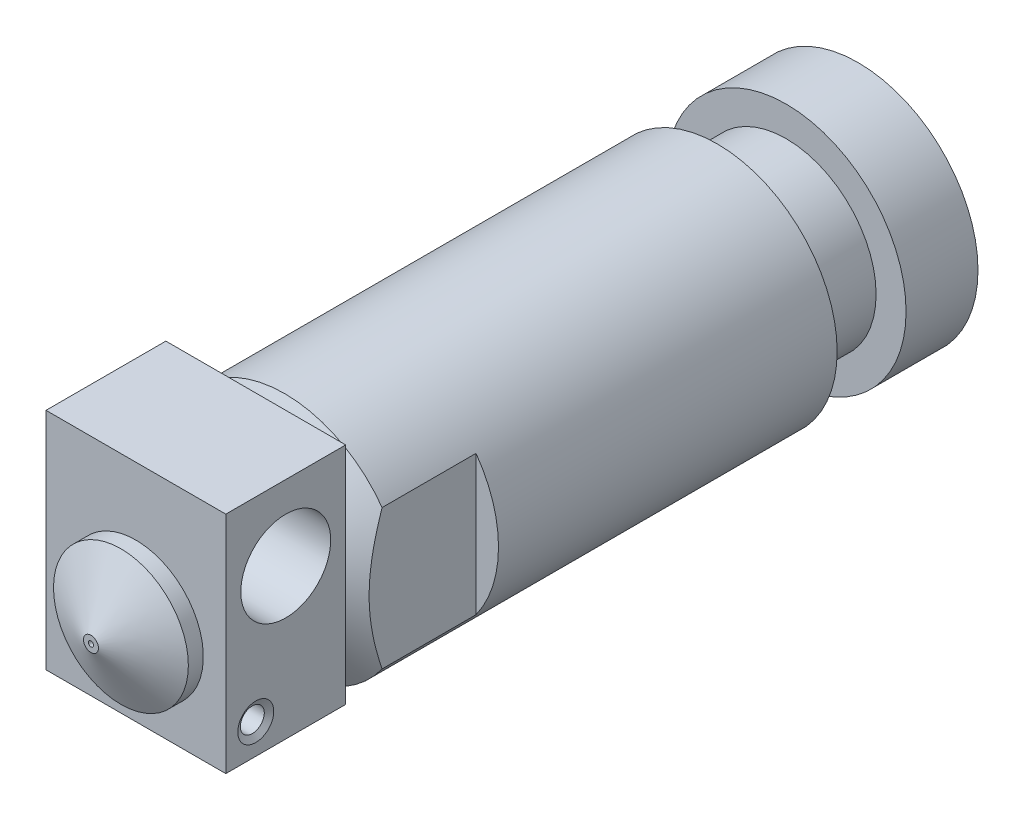
SolidWorks part; units mm, degrees
ref_plane "Plan de face" through (0, 0, 0) normal (0, 0, 1) x (1, 0, 0)
ref_plane "Plan de dessus" through (0, 0, 0) normal (0, 1, 0) x (1, 0, 0)
ref_plane "Plan de droite" through (0, 0, 0) normal (1, 0, 0) x (0, 0, -1)
sketch "Esquisse1" plane through (0, 0, 0) normal (0, 0, 1) x (1, 0, 0)
  circle A0 centre (0, 0) radius 8
  dimension "D1" = 16
extrude "Boss.-Extru.1" add sketch "Esquisse1" along normal blind 40
sketch "Esquisse2" plane through (0, 0, 0) normal (0, 0, -1) x (-1, 0, 0)
  circle A0 centre (0, 0) radius 6
  circle A1 centre (0, 0) radius 8
  dimension "D1" = 12
  dimension "D2" = 16
extrude "Enlèv. mat.-Extru.1" cut sketch "Esquisse2" against normal blind 4.6 from offset 4.8 offset against normal yes
chamfer "Chanfrein1" distance 3 angle 30 1 edges at (8, 0, 40)
sketch "Esquisse3" plane through (0, 0, 40) normal (0, 0, 1) x (1, 0, 0)
  line L1 (-8.5, 6) -> (-6.5, 6)
  line L2 (-8.5, 6) -> (-8.5, -6)
  line L3 (-8.5, -6) -> (-6.5, -6)
  line L4 (-6.5, 6) -> (-6.5, -6)
  line L5 (8.5, 6) -> (6.5, 6)
  line L6 (8.5, 6) -> (8.5, -6)
  line L7 (8.5, -6) -> (6.5, -6)
  line L8 (6.5, 6) -> (6.5, -6)
  dimension "D1" = 13
  dimension "D2" = 6.5
  dimension "D3" = 6
  dimension "D4" = 6
  dimension "D5" = 6
  dimension "D6" = 6
  dimension "D7" = 2
  dimension "D8" = 2
extrude "Enlèv. mat.-Extru.2" cut sketch "Esquisse3" against normal blind 8
sketch "Esquisse4" plane through (0, 0, 0) normal (0, 1, 0) x (1, 0, 0)
  line L0 (-5, -40) -> (5, -40) construction
  line L1 (-8, -9.4) -> (-8, -32) construction
  line L2 (0, 7.1809) -> (0, -45.3206) construction
  circle A0 centre (-5, -26.5) radius 1
  circle A1 centre (-5, -23.5) radius 1
  circle A2 centre (-5, -20.5) radius 1
  circle A3 centre (-5, -17.5) radius 1
  circle A4 centre (-5, -14.5) radius 1
  dimension "D2" = 2
  dimension "D3" = 2
  dimension "D4" = 2
  dimension "D5" = 2
  dimension "D9" = 2
  dimension "D1" = 13.5
  dimension "D6" = 3
  dimension "D7" = 3
  dimension "D8" = 3
  dimension "D10" = 3
  dimension "D11" = 3
revolve "Enlèvement de matière-Révolution1" cut sketch "Esquisse4" angle 360 about L2
sketch "Esquisse8" plane through (0, 0, 0) normal (0, 0, -1) x (-1, 0, 0)
  circle A0 centre (0, 0) radius 1
  dimension "D1" = 2
extrude "Enlèv. mat.-Extru.4" cut sketch "Esquisse8" against normal through all
sketch "Esquisse9" plane through (0, 0, 40) normal (0, 0, 1) x (1, 0, 0)
  circle A0 centre (0, 0) radius 4
  dimension "D1" = 8
extrude "Boss.-Extru.2" add sketch "Esquisse9" along normal blind 0.2
sketch "Esquisse10" plane through (0, 0, 40.2) normal (0, 0, 1) x (1, 0, 0)
  line L1 (6, 9) -> (-6, 9)
  line L2 (6, 9) -> (6, -6)
  line L3 (6, -6) -> (-6, -6)
  line L4 (-6, 9) -> (-6, -6)
  circle A0 centre (0, 0) radius 4 construction
  circle A1 centre (0, 0) radius 4 construction
  dimension "D3" = 6
  dimension "D1" = 15
  dimension "D2" = 12
  dimension "D4" = 6
extrude "Boss.-Extru.3" add sketch "Esquisse10" along normal blind 8
sketch "Esquisse11" plane through (6, 0, 0) normal (1, 0, 0) x (0, 0, -1)
  line L0 (-48.2, -6) -> (-48.2, 9) construction
  line L1 (-48.2, 9) -> (-40.2, 9) construction
  line L2 (-48.2, -6) -> (-40.2, -6) construction
  circle A0 centre (-44.2, 4) radius 3
  circle A1 centre (-46.2, -4) radius 0.7
  dimension "D1" = 6
  dimension "D4" = 1.4
  dimension "D2" = 4
  dimension "D3" = 5
  dimension "D5" = 2
  dimension "D6" = 2
extrude "Enlèv. mat.-Extru.5" cut sketch "Esquisse11" against normal through all contours A0
sketch "Esquisse13" plane through (6, 0, 0) normal (1, 0, 0) x (0, 0, -1)
  line L0 (-48.2, -6) -> (-48.2, 9) construction
  line L1 (-48.2, -6) -> (-40.2, -6) construction
  circle A0 centre (-46.2, -4) radius 0.8
  point P4 (-44.2, -6)
  dimension "D1" = 1.6
  dimension "D2" = 2
  dimension "D3" = 2
extrude "Enlèv. mat.-Extru.6" cut sketch "Esquisse13" against normal blind 3
chamfer "Chanfrein2" distance 0.4 angle 30 1 edges at (6, -3.2, 46.2)
sketch "Esquisse14" plane through (0, 0, 48.2) normal (0, 0, 1) x (1, 0, 0)
  circle A0 centre (0, 0) radius 4.5
  dimension "D1" = 9
  dimension "D2" = 0
extrude "Boss.-Extru.4" add sketch "Esquisse14" along normal blind 1
sketch "Esquisse15" plane through (0, 0, 49.2) normal (0, 0, 1) x (1, 0, 0)
  circle A0 centre (0, 0) radius 4.5
extrude "Boss.-Extru.5" add sketch "Esquisse15" along normal blind 2
chamfer "Chanfrein3" distance 2 distance2 4 1 edges at (4.5, 0, 51.2)
sketch "Esquisse16" plane through (0, 0, 51.2) normal (0, 0, 1) x (1, 0, 0)
  circle A0 centre (0, 0) radius 0.175
  dimension "D1" = 0.35
extrude "Enlèv. mat.-Extru.7" cut sketch "Esquisse16" against normal through all
